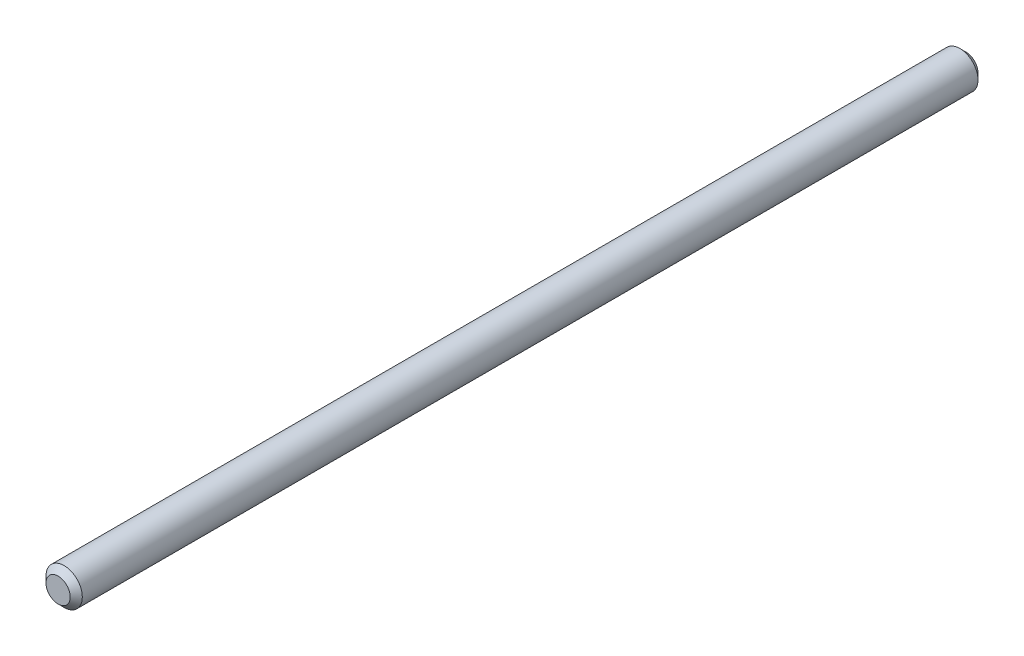
SolidWorks part; units mm, degrees
ref_plane "前基準面" through (0, 0, 0) normal (0, 0, 1) x (1, 0, 0)
ref_plane "上基準面" through (0, 0, 0) normal (0, 1, 0) x (1, 0, 0)
ref_plane "右基準面" through (0, 0, 0) normal (1, 0, 0) x (0, 0, -1)
sketch "草圖1" plane through (0, 0, 0) normal (0, 0, 1) x (1, 0, 0)
  circle A0 centre (0, 0) radius 3
  dimension "D1" = 6
extrude "填料-伸長1" add sketch "草圖1" along normal blind 150
chamfer "導角1" distance 1 angle 45 2 edges at (3, 0, 0) (3, 0, 150)
